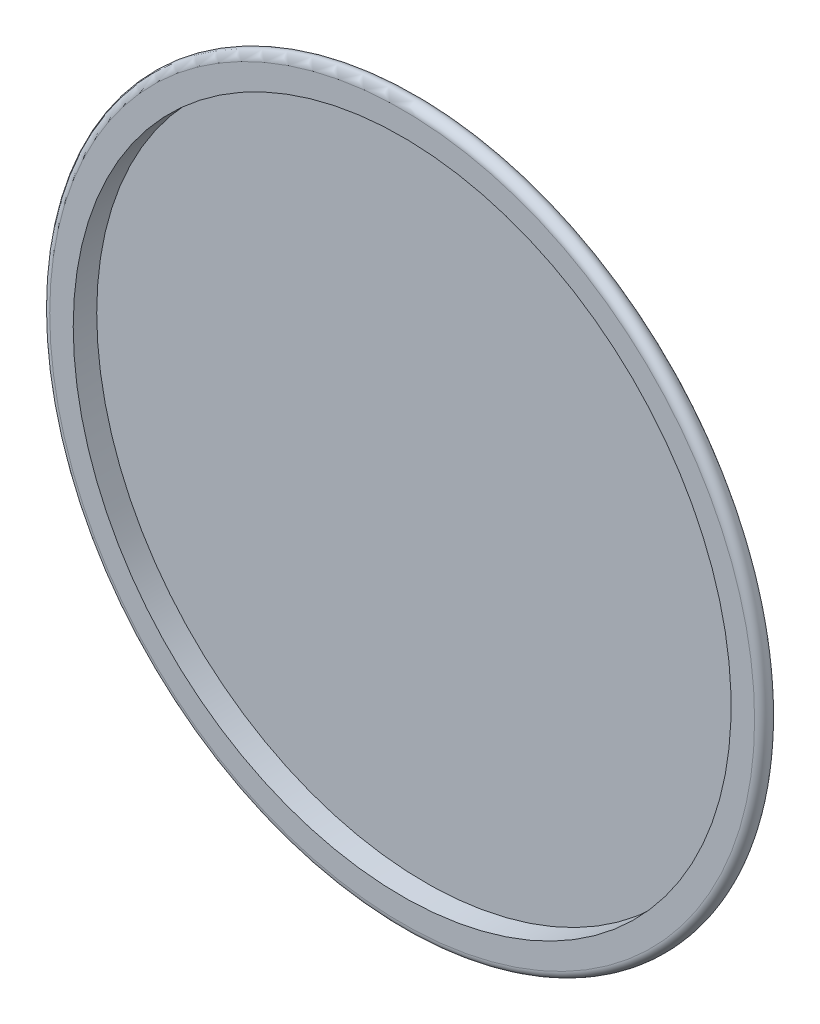
SolidWorks part; units mm, degrees
ref_plane "Front Plane" through (0, 0, 0) normal (0, 0, 1) x (1, 0, 0)
ref_plane "Top Plane" through (0, 0, 0) normal (0, 1, 0) x (1, 0, 0)
ref_plane "Right Plane" through (0, 0, 0) normal (1, 0, 0) x (0, 0, -1)
sketch "Croquis1" plane through (0, 0, 0) normal (0, 1, 0) x (1, 0, 0)
  line L0 (21, 0) -> (22.5, 0)
  line L1 (21, 0) -> (21, 1.5)
  line L2 (21, 1.5) -> (0, 1.5)
  line L3 (20, 2) -> (0, 2)
  line L4 (0, 2) -> (0, 1.5)
  arc A0 (22.5, 0) -> (22.8159, 0.8876) centre (22.5, 0.5) ccw
  arc A1 (22.8159, 0.8876) -> (20, 2) centre (19.6571, -2.9882) ccw
  dimension "D1" = 1.5
  dimension "D4" = 0.5
  dimension "D2" = 5
  dimension "D3" = 21
  dimension "D5" = 20
  dimension "D6" = 22.5
  dimension "D7" = 0.5
revolve "Revolución1" add sketch "Croquis1" angle 360 about L4
